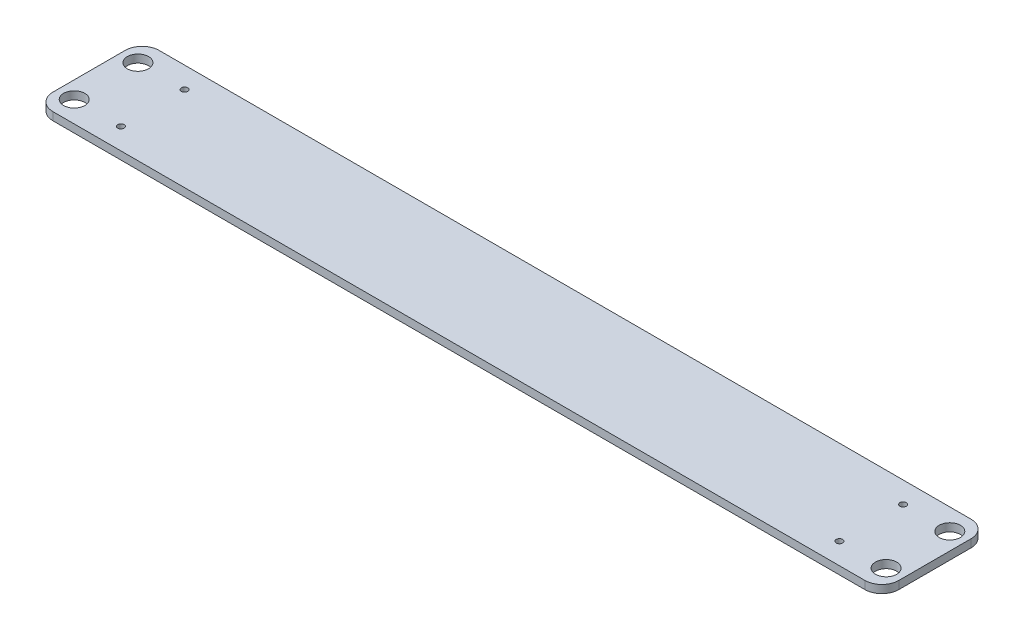
SolidWorks part; units mm, degrees
ref_plane "Front Plane" through (0, 0, 0) normal (0, 0, 1) x (1, 0, 0)
ref_plane "Top Plane" through (0, 0, 0) normal (0, 1, 0) x (1, 0, 0)
ref_plane "Right Plane" through (0, 0, 0) normal (1, 0, 0) x (0, 0, -1)
sketch "Sketch1" plane through (0, 0, 0) normal (0, 1, 0) x (1, 0, 0)
  line L0 (0, -31.75) -> (1.27, -31.75) construction
  line L1 (10.16, 0) -> (253.0475, 0)
  line L2 (0, -10.16) -> (0, -26.035)
  line L3 (10.16, -63.5) -> (253.0475, -63.5)
  line L7 (0, -43.815) -> (0, -53.34)
  line L8 (19.05, -31.75) -> (87.4324, -31.75) construction
  line L14 (0, -43.815) -> (0, -26.035)
  line L18 (253.0475, 0) -> (253.0475, -63.5)
  circle A0 centre (10.16, -50.8) radius 6.35
  circle A1 centre (10.16, -12.7) radius 6.35
  circle A3 centre (10.16, -12.7) radius 6.35 construction
  circle A4 centre (10.16, -50.8) radius 6.35 construction
  arc A5 (0, -53.34) -> (10.16, -63.5) centre (10.16, -53.34) ccw
  arc A6 (10.16, 0) -> (0, -10.16) centre (10.16, -10.16) ccw
  circle A7 centre (38.1, -50.8) radius 1.905
  circle A8 centre (38.1, -12.7) radius 1.905
  point P1 (10.16, -50.8)
  point P3 (35.8988, -50.8)
  point P9 (38.1, -50.8)
  point P22 (0, -63.5)
  point P25 (0, 0)
  point P38 (50.8, -69.85)
  dimension "D3" = 19.05
  dimension "D4" = 12.7
  dimension "D5" = 19.05
  dimension "D10" = 31.75
  dimension "D11" = 12.7
  dimension "D12" = 12.7
  dimension "D13" = 10.16
  dimension "D14" = 3.81
  dimension "D15" = 3.81
  dimension "D8" = 38.1
  dimension "D1" = 63.5
  dimension "D2" = 253.0475
  dimension "D6" = 10.16
  dimension "D7" = 10.16
  dimension "D9" = 38.1
  dimension "D16" = 12.7
extrude "Boss-Extrude1" add sketch "Sketch1" along normal blind 4.7625
mirror "Mirror1" about plane through (253.0475, 4.7625, 0) normal (-1, 0, 0) of "Boss-Extrude1"
